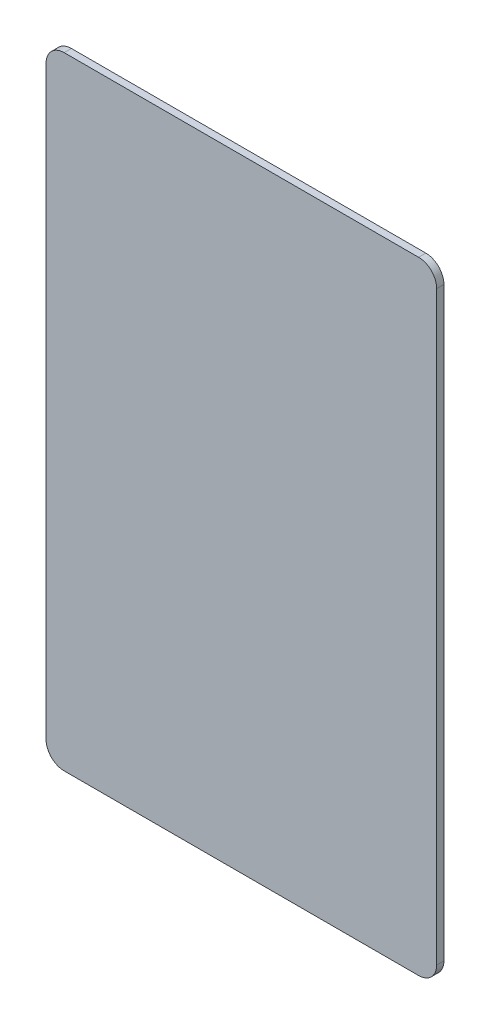
SolidWorks part; units mm, degrees
ref_plane "Płaszczyzna przednia" through (0, 0, 0) normal (0, 0, 1) x (1, 0, 0)
ref_plane "Płaszczyzna górna" through (0, 0, 0) normal (0, 1, 0) x (1, 0, 0)
ref_plane "Płaszczyzna prawa" through (0, 0, 0) normal (1, 0, 0) x (0, 0, -1)
sketch "Szkic1" plane through (0, 0, 0) normal (0, 0, 1) x (1, 0, 0)
  line L1 (-24.5, 43) -> (24.5, 43)
  line L2 (-27, 40.5) -> (-27, -40.5)
  line L3 (-24.5, -43) -> (24.5, -43)
  line L4 (27, 40.5) -> (27, -40.5)
  line L5 (-27, 43) -> (27, -43) construction
  line L6 (-27, -43) -> (27, 43) construction
  arc A0 (24.5, 43) -> (27, 40.5) centre (24.5, 40.5) cw
  arc A1 (24.5, -43) -> (27, -40.5) centre (24.5, -40.5) ccw
  arc A2 (-27, -40.5) -> (-24.5, -43) centre (-24.5, -40.5) ccw
  arc A3 (-24.5, 43) -> (-27, 40.5) centre (-24.5, 40.5) ccw
  point P0 (0, 0)
  dimension "D3" = 2.5
  dimension "D1" = 54
  dimension "D2" = 86
extrude "Dodanie-wyciągnięcie1" add sketch "Szkic1" along normal blind 1
sketch "Szkic2" plane through (0, 0, 1) normal (0, 0, 1) x (1, 0, 0)
  line L0 (0, -43) -> (0, 43) construction
  line L1 (-24.5, -43) -> (24.5, -43) construction
  line L2 (24.5, 43) -> (-24.5, 43) construction
  circle A0 centre (0, -8) radius 22.5 construction
  dimension "D1" = 45
  dimension "D2" = 35
